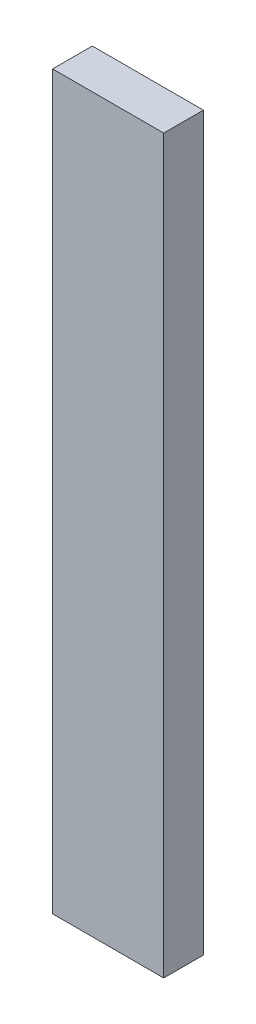
SolidWorks part; units mm, degrees
ref_plane "Front Plane" through (0, 0, 0) normal (0, 0, 1) x (1, 0, 0)
ref_plane "Top Plane" through (0, 0, 0) normal (0, 1, 0) x (1, 0, 0)
ref_plane "Right Plane" through (0, 0, 0) normal (1, 0, 0) x (0, 0, -1)
sketch "Sketch1" plane through (0, 0, 0) normal (0, 1, 0) x (1, 0, 0)
  line L1 (-0.35, 0.125) -> (0.35, 0.125)
  line L2 (-0.35, 0.125) -> (-0.35, -0.125)
  line L3 (-0.35, -0.125) -> (0.35, -0.125)
  line L4 (0.35, 0.125) -> (0.35, -0.125)
  line L5 (-0.35, 0.125) -> (0.35, -0.125) construction
  line L6 (-0.35, -0.125) -> (0.35, 0.125) construction
  point P0 (0, 0)
  dimension "D1" = 0.7
  dimension "D2" = 0.25
extrude "Boss-Extrude1" add sketch "Sketch1" along normal blind 4.61
